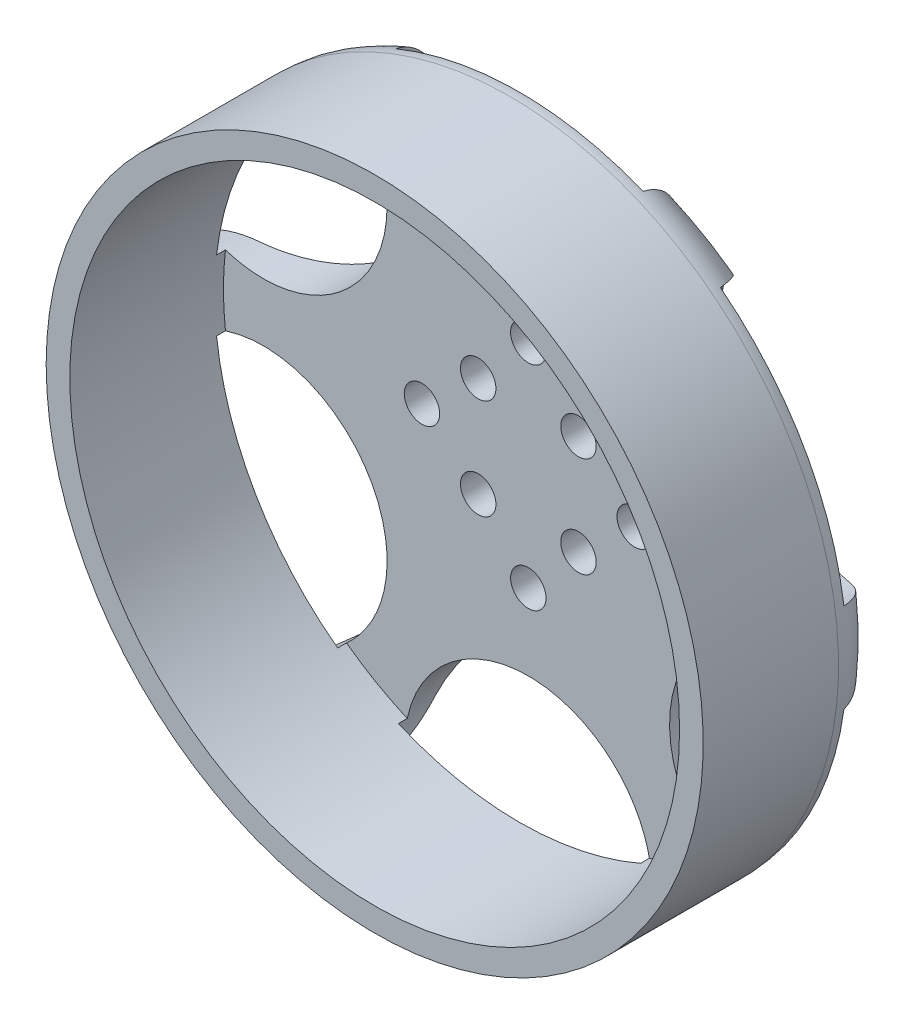
SolidWorks part; units mm, degrees
ref_plane "Front Plane" through (0, 0, 0) normal (0, 0, 1) x (1, 0, 0)
ref_plane "Top Plane" through (0, 0, 0) normal (0, 1, 0) x (1, 0, 0)
ref_plane "Right Plane" through (0, 0, 0) normal (1, 0, 0) x (0, 0, -1)
ref_axis "Axis1" through (0, 0, -88.99) along (0, 0, 1)
sketch "Sketch2" plane through (0, 0, 0) normal (0, 1, 0) x (1, 0, 0)
  line L0 (0, 32) -> (-2, 32)
  line L1 (0, 88.99) -> (0, -88.99) construction
  line L2 (-2, 32) -> (-2, 27)
  line L3 (-2, 27) -> (-27.8, 27)
  line L4 (-27.8, 27) -> (-27.8, 8.25)
  line L5 (-27.8, 8.25) -> (0, 8.25)
  line L6 (0, 8.25) -> (0, 32)
  dimension "D1" = 2
  dimension "D2" = 27.8
  dimension "D3" = 32
  dimension "D4" = 27
  dimension "D5" = 8.25
revolve "Revolve1" add sketch "Sketch2" angle 360 about axis through (0, 0, -88.99) along (0, 0, 1)
sketch "Sketch3" plane through (0, 0, -27) normal (0, 0, -1) x (-1, 0, 0)
  line L0 (0, 0) -> (0, 50000) construction
  line L1 (0, 0) -> (50000, 0) construction
  line L2 (0, 9) -> (0, 0) construction
  line L3 (0, 0) -> (4.2426, 4.2426) construction
  circle A0 centre (0, 9) radius 1.5
  circle A1 centre (4.2426, 4.2426) radius 1.5
  dimension "D4" = 3
  dimension "D5" = 3
  dimension "D1" = 45
  dimension "D2" = 6
  dimension "D3" = 9
extrude "Cut-Extrude1" cut sketch "Sketch3" against normal through all
pattern_circular "CirPattern1" count 4 over 360 about axis through (0, 0, 0) along (0, 0, 1) of "Cut-Extrude1"
chamfer "Chamfer1" distance 4.5 angle 70 1 edges at (-27.8, 0, -27)
fillet "Fillet1" radius 4 1 edges at (-27.8, 0, -22.5)
sketch "Sketch4" plane through (0, 0, -8.25) normal (0, 0, 1) x (1, 0, 0)
  circle A0 centre (0, 0) radius 25.8
  circle A1 centre (0, 0) radius 27.8 construction
  dimension "D1" = 2
extrude "Cut-Extrude2" cut sketch "Sketch4" against normal blind 13
sketch "Sketch5" plane through (0, 0, -27) normal (0, 0, -1) x (-1, 0, 0)
  line L0 (0, -1000) -> (0, 49000) construction
  circle A0 centre (0, 0) radius 15.4364 construction
  circle A2 centre (0, 0) radius 27.8 construction
  ellipse E0 centre (0, 25.7576) end of major axis (-10.4588, 25.7576) minor radius 10.3212
  point P4 (0, 0)
  point P12 (14.7204, 34.7827)
  point P13 (-11.1963, 22.5405)
  point P14 (0, 39.0333)
  point P15 (12.3887, 27.6681)
  point P16 (0, 33.3233)
  point P17 (-7.0856, 24.1501)
  point P18 (0, 55.0149)
  point P19 (15.8759, 35.1013)
  point P20 (0, 0)
  point P21 (11.2985, 34.5892)
  point P22 (0, 29.5677)
  point P23 (-10.4588, 25.7576)
extrude "Cut-Extrude3" cut sketch "Sketch5" against normal blind 6.5
pattern_circular "CirPattern2" count 6 over 360 about axis through (0, 0, -88.99) along (0, 0, 1) of "Cut-Extrude3"
